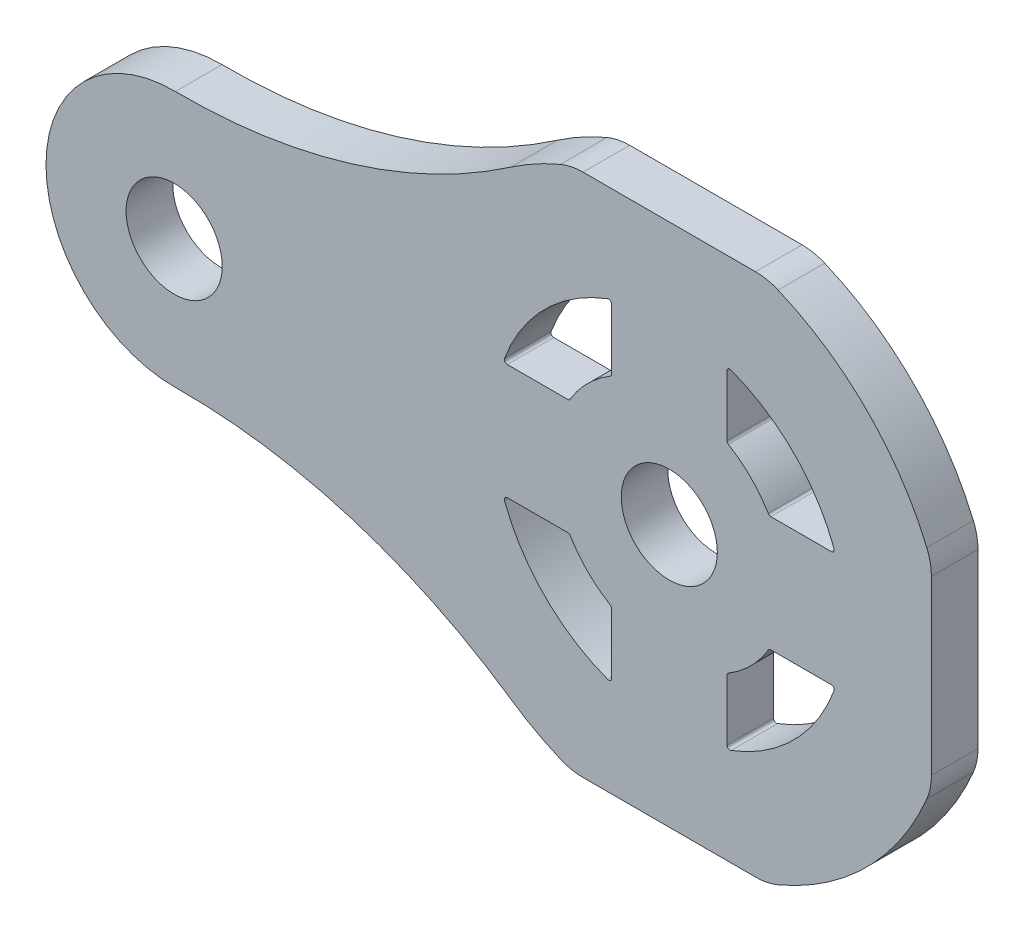
SolidWorks part; units mm, degrees
ref_plane "Plane1" through (0, 0, 0) normal (0, 0, 1) x (1, 0, 0)
ref_plane "Plane2" through (0, 0, 0) normal (0, 1, 0) x (1, 0, 0)
ref_plane "Plane3" through (0, 0, 0) normal (1, 0, 0) x (0, 0, -1)
sketch "Sketch1" plane through (0, 0, 0) normal (0, 0, 1) x (1, 0, 0)
  line L0 (0, 0) -> (-40, 0) construction
  line L1 (-9.9, 27.8196) -> (-9.9, 17.4336)
  line L2 (-17.4336, 9.9) -> (-27.8196, 9.9)
  line L3 (0, -45) -> (0, 45) construction
  line L4 (17.4336, 9.9) -> (27.8196, 9.9)
  line L5 (45, 14.7986) -> (45, -14.7986)
  line L6 (-14.7986, 45) -> (14.7986, 45)
  line L7 (-14.7986, -45) -> (14.7986, -45)
  line L8 (9.9, 27.8196) -> (9.9, 17.4336)
  line L9 (9.9, -27.8196) -> (9.9, -17.4336)
  line L10 (17.4336, -9.9) -> (27.8196, -9.9)
  line L11 (-17.4336, -9.9) -> (-27.8196, -9.9)
  line L12 (-9.9, -27.8196) -> (-9.9, -17.4336)
  arc A0 (28.2879, 10.5751) -> (10.5751, 28.2879) centre (0, 0) ccw
  arc A1 (-27.1765, 39.5656) -> (-84.7825, 21.9989) centre (-83.7941, 121.994) cw
  arc A2 (-27.1765, -39.5656) -> (-84.7825, -21.9989) centre (-83.7941, -121.994) ccw
  arc A3 (-84.7825, 21.9989) -> (-107, 0) centre (-85, 0) ccw
  arc A4 (-84.7825, -21.9989) -> (-107, 0) centre (-85, 0) cw
  arc A5 (-27.1765, -39.5656) -> (-18.693, -44.2105) centre (0, 0) ccw
  arc A6 (-10.5751, 28.2879) -> (-28.2879, 10.5751) centre (0, 0) ccw
  arc A7 (17.0042, -10.1438) -> (10.1438, -17.0042) centre (0, 0) cw
  arc A8 (-10.1438, -17.0042) -> (-17.0042, -10.1438) centre (0, 0) cw
  circle A9 centre (-85, 0) radius 8.25
  arc A10 (18.693, -44.2105) -> (44.2105, -18.693) centre (0, 0) ccw
  arc A11 (-10.5751, -28.2879) -> (-28.2879, -10.5751) centre (0, 0) cw
  arc A12 (-10.1438, 17.0042) -> (-17.0042, 10.1438) centre (0, 0) ccw
  arc A13 (44.2105, 18.693) -> (18.693, 44.2105) centre (0, 0) ccw
  arc A14 (-18.693, 44.2105) -> (-27.1765, 39.5656) centre (0, 0) ccw
  arc A15 (17.0042, 10.1438) -> (10.1438, 17.0042) centre (0, 0) ccw
  arc A16 (28.2879, -10.5751) -> (10.5751, -28.2879) centre (0, 0) cw
  circle A17 centre (0, 0) radius 8.25
  arc A18 (-9.9, 27.8196) -> (-10.5751, 28.2879) centre (-10.4, 27.8196) ccw
  arc A19 (-27.8196, 9.9) -> (-28.2879, 10.5751) centre (-27.8196, 10.4) cw
  arc A20 (-17.0042, 10.1438) -> (-17.4336, 9.9) centre (-17.4336, 10.4) cw
  arc A21 (-10.1438, 17.0042) -> (-9.9, 17.4336) centre (-10.4, 17.4336) ccw
  arc A22 (9.9, 27.8196) -> (10.5751, 28.2879) centre (10.4, 27.8196) cw
  arc A23 (9.9, 17.4336) -> (10.1438, 17.0042) centre (10.4, 17.4336) ccw
  arc A24 (17.4336, 9.9) -> (17.0042, 10.1438) centre (17.4336, 10.4) cw
  arc A25 (27.8196, 9.9) -> (28.2879, 10.5751) centre (27.8196, 10.4) ccw
  arc A26 (17.0042, -10.1438) -> (17.4336, -9.9) centre (17.4336, -10.4) cw
  arc A27 (28.2879, -10.5751) -> (27.8196, -9.9) centre (27.8196, -10.4) ccw
  arc A28 (10.5751, -28.2879) -> (9.9, -27.8196) centre (10.4, -27.8196) cw
  arc A29 (10.1438, -17.0042) -> (9.9, -17.4336) centre (10.4, -17.4336) ccw
  arc A30 (-10.1438, -17.0042) -> (-9.9, -17.4336) centre (-10.4, -17.4336) cw
  arc A31 (-10.5751, -28.2879) -> (-9.9, -27.8196) centre (-10.4, -27.8196) ccw
  arc A32 (-28.2879, -10.5751) -> (-27.8196, -9.9) centre (-27.8196, -10.4) cw
  arc A33 (-17.0042, -10.1438) -> (-17.4336, -9.9) centre (-17.4336, -10.4) ccw
  arc A34 (-14.7986, -45) -> (-18.693, -44.2105) centre (-14.7986, -35) cw
  arc A35 (14.7986, -45) -> (18.693, -44.2105) centre (14.7986, -35) ccw
  arc A36 (45, -14.7986) -> (44.2105, -18.693) centre (35, -14.7986) cw
  arc A37 (45, 14.7986) -> (44.2105, 18.693) centre (35, 14.7986) ccw
  arc A38 (14.7986, 45) -> (18.693, 44.2105) centre (14.7986, 35) cw
  arc A39 (-14.7986, 45) -> (-18.693, 44.2105) centre (-14.7986, 35) ccw
  point P40 (-9.9, 28.5312)
  point P43 (-28.5312, 9.9)
  point P46 (-17.1473, 9.9)
  point P49 (-9.9, 17.1473)
  point P52 (9.9, 28.5312)
  point P55 (9.9, 17.1473)
  point P58 (17.1473, 9.9)
  point P61 (28.5312, 9.9)
  point P64 (17.1473, -9.9)
  point P67 (28.5312, -9.9)
  point P70 (9.9, -28.5312)
  point P73 (9.9, -17.1473)
  point P76 (-9.9, -17.1473)
  point P79 (-9.9, -28.5312)
  point P82 (-28.5312, -9.9)
  point P85 (-17.1473, -9.9)
  point P90 (16.7033, -45)
  point P93 (45, -16.7033)
  point P96 (45, 16.7033)
  point P99 (16.7033, 45)
  point P102 (-16.7033, 45)
  dimension "D2" = 30.2
  dimension "D3" = 48
  dimension "D5" = 9.9
  dimension "D6" = 22
  dimension "D8" = 100
  dimension "D9" = 16.5
  dimension "D10" = 45
  dimension "D13" = 19.8
  dimension "D14" = 16.5
  dimension "D15" = 0.5
  dimension "D16" = 10
  dimension "D4" = 85
  dimension "D7" = 9.9
  dimension "D11" = 90
extrude "Base-Extrude" add sketch "Sketch1" along normal blind 8
chamfer "Chamfer1" [suppressed] distance 7.5 angle 45
